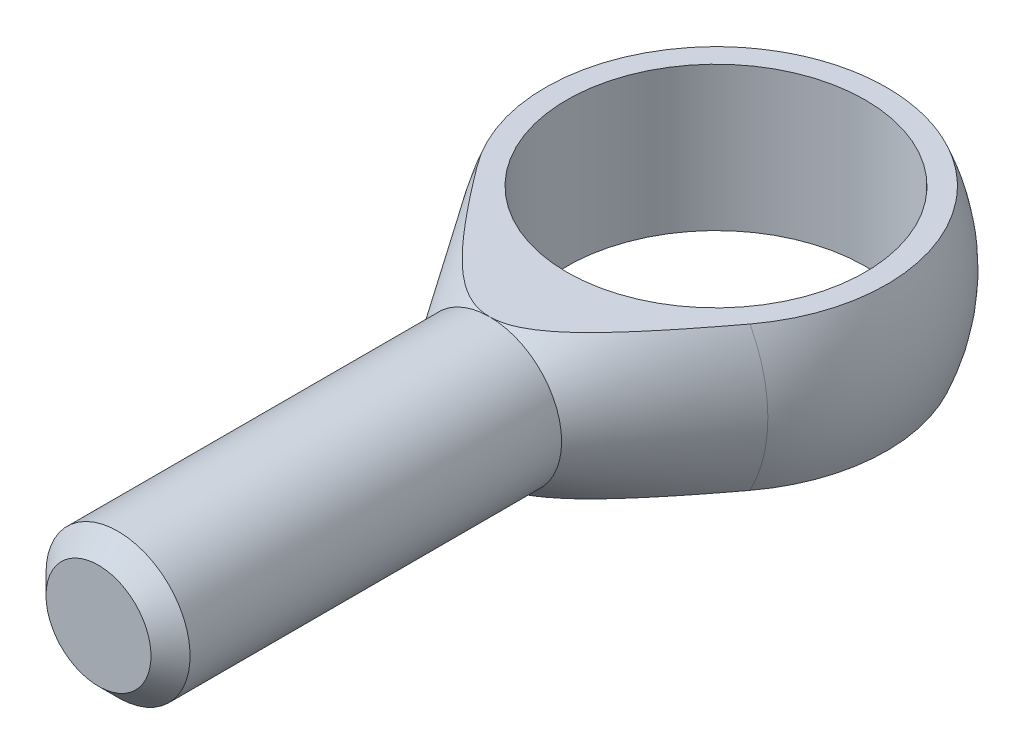
SolidWorks part; units mm, degrees
material "1.0545 (S355N)"
ref_plane "Płaszczyzna przednia" through (0, 0, 0) normal (0, 0, 1) x (1, 0, 0)
ref_plane "Płaszczyzna górna" through (0, 0, 0) normal (0, 1, 0) x (1, 0, 0)
ref_plane "Płaszczyzna prawa" through (0, 0, 0) normal (1, 0, 0) x (0, 0, -1)
sketch "Szkic1" plane through (0, 0, 0) normal (0, 1, 0) x (1, 0, 0)
  line L0 (0, 26.0435) -> (0, -71.4286) construction
  line L1 (-7, -60) -> (7, -60)
  line L2 (7, -60) -> (7, -22)
  line L3 (-7, -60) -> (-7, -22)
  line L4 (-14.9961, -9.9558) -> (-7, -22)
  line L5 (7, -22) -> (14.9961, -9.9558)
  line L6 (-7, -22) -> (7, -22)
  line L7 (0, 18) -> (0, -60)
  arc A0 (14.9961, -9.9558) -> (-14.9961, -9.9558) centre (0, 0) ccw
  point P7 (0, -60)
  dimension "d4" = 36
  dimension "d2" = 14
  dimension "l1" = 60
  dimension "l3" = 38
revolve "Obrót1" add sketch "Szkic1" angle 360 about L0
sketch "Szkic2" plane through (0, 0, 0) normal (1, 0, 0) x (0, 0, -1)
  line L4 (-22, 7) -> (16.5831, 7)
  line L5 (-22, -7) -> (16.5831, -7)
  line L6 (-22, -7) -> (-9.9558, -14.9961) construction
  line L7 (-9.9558, 14.9961) -> (-22, 7) construction
  line L8 (-22, -7) -> (-9.9558, -14.9961)
  line L9 (-9.9558, 14.9961) -> (-22, 7)
  arc A0 (-9.9558, -14.9961) -> (-9.9558, 14.9961) centre (0, 0) ccw construction
  arc A1 (-9.9558, -14.9961) -> (16.5831, -7) centre (0, 0) ccw
  arc A2 (16.5831, 7) -> (-9.9558, 14.9961) centre (0, 0) ccw
extrude "Wytnij-wyciągnięcie1" cut sketch "Szkic2" against normal through all both and the other way through all
sketch "Szkic3" plane through (0, 0, 0) normal (0, 1, 0) x (1, 0, 0)
  circle A0 centre (0, 0) radius 14.5
  dimension "b" = 29
extrude "Wytnij-wyciągnięcie2" cut sketch "Szkic3" against normal through all both and the other way through all contours A0
chamfer "Sfazowanie1" distance 1.9 angle 45 1 edges at (-7, 0, 60)
equation "\"D1@Sfazowanie1\"=\"l3@Szkic1\"*0.05"
